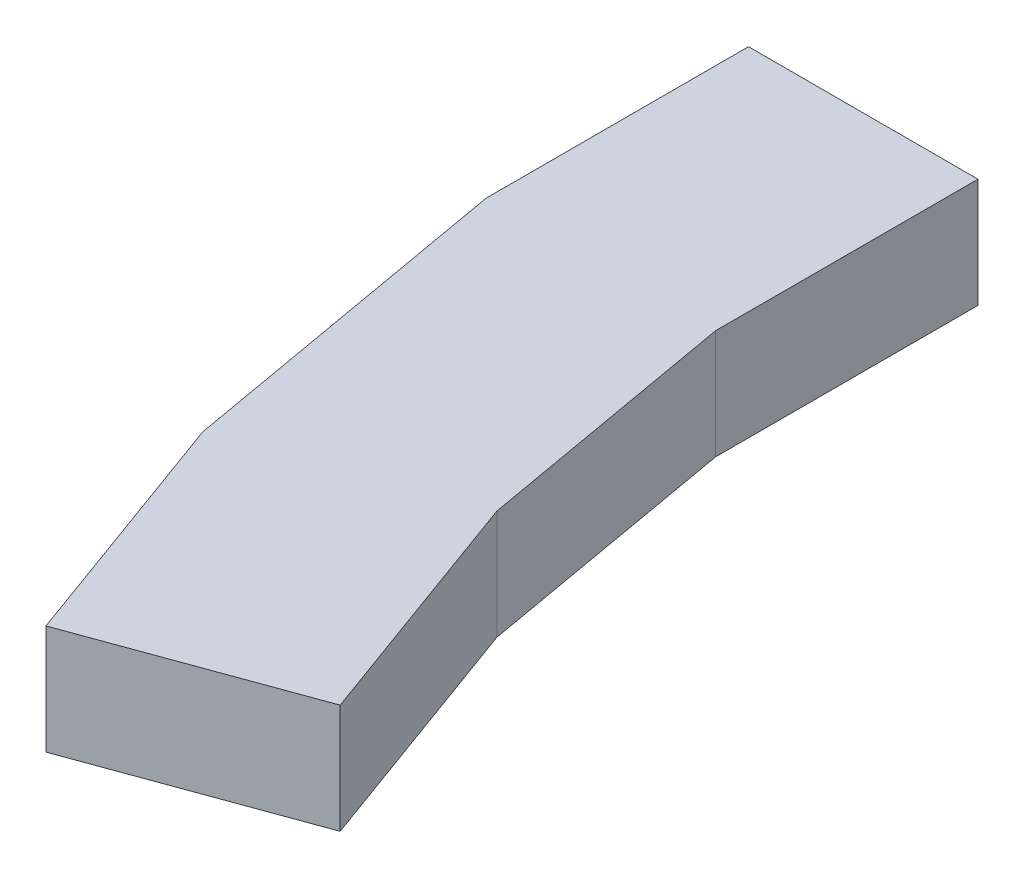
SolidWorks part; units mm, degrees
ref_plane "Front Plane" through (0, 0, 0) normal (0, 0, 1) x (1, 0, 0)
ref_plane "Top Plane" through (0, 0, 0) normal (0, 1, 0) x (1, 0, 0)
ref_plane "Right Plane" through (0, 0, 0) normal (1, 0, 0) x (0, 0, -1)
sketch "Sketch1" plane through (0, 76.0424, 0) normal (0, 1, 0) x (1, 0, 0)
  line L0 (37.1122, 12.5) -> (42.6647, -18.9895)
  line L3 (42.6647, -18.9895) -> (50.8732, -41.5422)
  line L4 (50.8732, -41.5422) -> (70.6067, -34.3597)
  line L6 (70.6067, -34.3597) -> (62.3982, -11.8071)
  line L7 (62.3982, -11.8071) -> (58.1122, 12.5)
  line L8 (58.1122, 12.5) -> (58.1122, 36.5)
  line L9 (58.1122, 60.5) -> (58.1122, 12.5) construction
  line L10 (58.1122, 36.5) -> (37.1122, 36.5)
  line L11 (37.1122, 60.5) -> (37.1122, 12.5) construction
  line L12 (37.1122, 36.5) -> (37.1122, 12.5)
  point P3 (64.4787, -4.9916)
  point P4 (48.3917, -18.4902)
  point P5 (79.9056, -23.3767)
  point P6 (64.0708, -37.7727)
  point P7 (48.7066, -18.226)
  point P10 (0, 0)
  point P11 (48.3917, -18.4902)
  point P13 (64.4787, -4.9916)
  point P22 (79.9056, -23.3767)
  point P23 (50.8935, -42.4388)
  point P24 (70.6067, -34.3597)
  point P25 (42.6647, -18.9895)
  point P26 (50.8732, -41.5422)
  point P27 (39.0435, -10.6116)
  point P28 (42.6647, -18.9895)
  point P29 (69.0404, 7.4067)
  point P30 (62.3982, -11.8071)
  point P31 (65.1949, -19.4909)
  point P32 (70.6067, -34.3597)
extrude "Boss-Extrude1" add sketch "Sketch1" along normal blind 10
